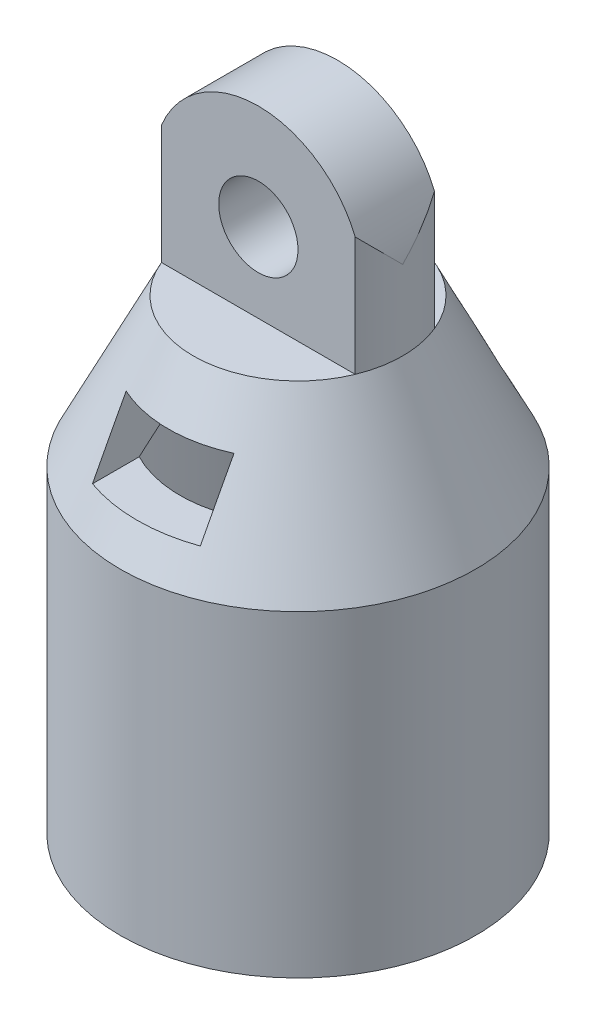
SolidWorks part; units mm, degrees
ref_plane "Front Plane" through (0, 0, 0) normal (0, 0, 1) x (1, 0, 0)
ref_plane "Top Plane" through (0, 0, 0) normal (0, 1, 0) x (1, 0, 0)
ref_plane "Right Plane" through (0, 0, 0) normal (1, 0, 0) x (0, 0, -1)
sketch "Sketch1" plane through (0, 0, 0) normal (0, 1, 0) x (1, 0, 0)
  circle A0 centre (0, 0) radius 6.096
  circle A2 centre (0, 0) radius 7.112
extrude "Boss-Extrude1" add sketch "Sketch1" along normal blind 12.7
sketch "Sketch2" plane through (0, 0, 0) normal (0, 0, 1) x (1, 0, 0)
  line L10 (-7.112, 12.7) -> (-6.096, 12.7)
  line L11 (7.112, 12.7) -> (-7.112, 12.7) construction
  line L13 (0, 16.602) -> (0, 18.634)
  line L15 (-6.096, 12.7) -> (-2.159, 16.602)
  line L16 (-2.159, 16.602) -> (0, 16.602)
  line L18 (0, 18.634) -> (-4.191, 18.634)
  line L19 (-4.191, 18.634) -> (-7.112, 12.7)
revolve "Revolve2" add sketch "Sketch2" angle 360 about L13
sketch "Sketch3" plane through (0, 0, 0) normal (0, 0, 1) x (1, 0, 0)
  line L7 (-4.191, 18.634) -> (-4.191, 21.809)
  line L9 (-4.191, 18.634) -> (4.191, 18.634)
  line L10 (4.191, 18.634) -> (-4.191, 18.634) construction
  line L11 (4.191, 18.634) -> (4.191, 21.809)
  circle A2 centre (0, 21.809) radius 1.5875
  arc A3 (-4.191, 21.809) -> (4.191, 21.809) centre (0, 21.809) cw
extrude "Boss-Extrude3" add sketch "Sketch3" along normal mid plane 3.175
sketch "Sketch4" plane through (0, 0, 0) normal (0, 0, 1) x (1, 0, 0)
  line L4 (0, 16.602) -> (2.159, 16.602)
  line L5 (-2.159, 16.602) -> (-2.159, 14.062)
  line L16 (0, 16.602) -> (-2.159, 16.602)
  line L17 (2.159, 16.602) -> (2.159, 14.062)
  line L18 (2.159, 14.062) -> (-2.159, 14.062)
extrude "Cut-Extrude1" cut sketch "Sketch4" along normal mid plane 25.4
sketch "Sketch5" plane through (0, 18.634, 0) normal (0, -1, 0) x (1, 0, 0)
  circle A0 centre (0, 0) radius 4.191
  circle A1 centre (0, 0) radius 4.4816
extrude "Cut-Extrude3" cut sketch "Sketch5" against normal blind 25.4 flip side to cut contours A0
